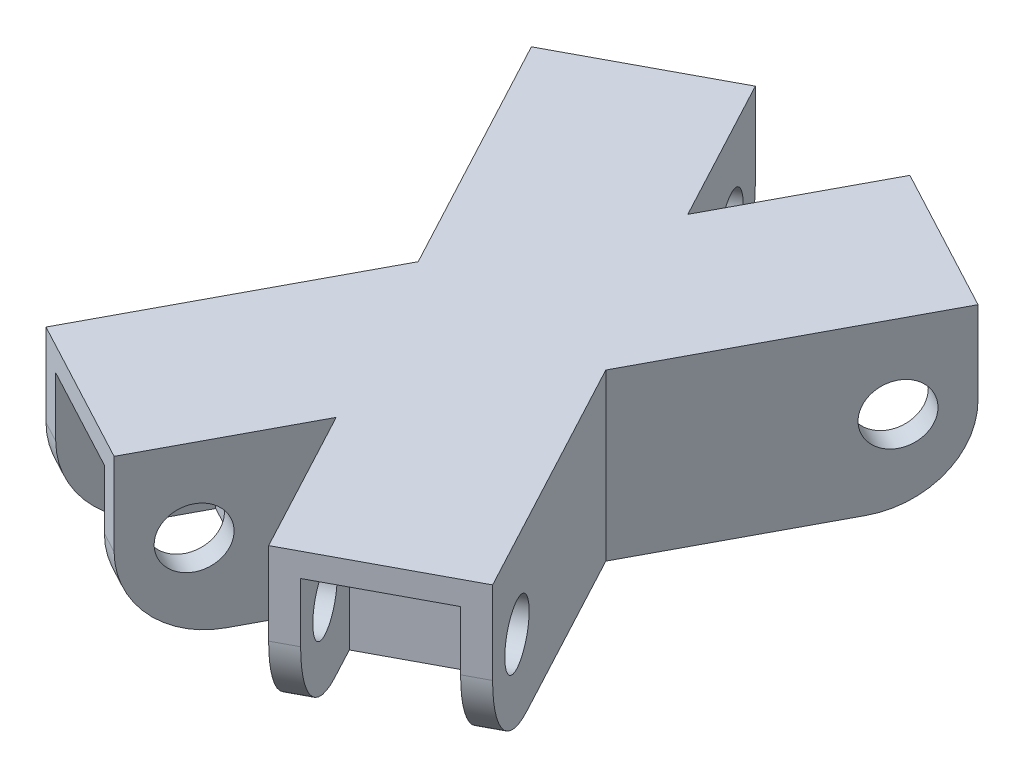
SolidWorks part; units mm, degrees
ref_plane "Front Plane" through (0, 0, 0) normal (0, 0, 1) x (1, 0, 0)
ref_plane "Top Plane" through (0, 0, 0) normal (0, 1, 0) x (1, 0, 0)
ref_plane "Right Plane" through (0, 0, 0) normal (1, 0, 0) x (0, 0, -1)
sketch "Sketch1" plane through (0, 0, 0) normal (0, 1, 0) x (1, 0, 0)
  line L0 (0, 0) -> (29.8937, 56.0234) construction
  line L1 (0, 0) -> (82.5536, 0) construction
  line L2 (0, 0) -> (-29.8937, -56.0234) construction
  line L3 (0, 0) -> (-29.8937, 56.0234) construction
  line L4 (0, 0) -> (-62.1107, 0) construction
  line L5 (0, 0) -> (29.8937, -56.0234) construction
  line L6 (-29.8937, 56.0234) -> (-18.689, 62.0021) construction
  line L7 (-29.8937, 56.0234) -> (-41.0984, 50.0446) construction
  line L8 (-41.0984, 50.0446) -> (-14.3949, 0) construction
  line L9 (-18.689, 62.0021) -> (0, 26.9773) construction
  line L10 (18.689, -62.0021) -> (41.0984, -50.0446) construction
  line L11 (29.8937, 56.0234) -> (18.689, 62.0021) construction
  line L12 (29.8937, 56.0234) -> (41.0984, 50.0446) construction
  line L13 (18.689, 62.0021) -> (0, 26.9773) construction
  line L14 (41.0984, 50.0446) -> (14.3949, 0) construction
  line L15 (-29.8937, -56.0234) -> (-18.689, -62.0021) construction
  line L16 (-29.8937, -56.0234) -> (-41.0984, -50.0446) construction
  line L17 (-14.3949, 0) -> (-41.0984, -50.0446) construction
  line L18 (14.3949, 0) -> (41.0984, -50.0446) construction
  line L19 (0, -26.9773) -> (18.689, -62.0021) construction
  line L20 (0, -26.9773) -> (-18.689, -62.0021) construction
  line L21 (47.9717, 52.135) -> (20.1528, 0)
  line L22 (20.1528, 0) -> (47.9717, -52.135)
  line L23 (16.5987, -68.8755) -> (47.9717, -52.135)
  line L24 (0, -37.7682) -> (16.5987, -68.8755)
  line L25 (0, -37.7682) -> (-16.5987, -68.8755)
  line L26 (-32.2852, -60.5052) -> (-16.5987, -68.8755)
  line L27 (-32.2852, -60.5052) -> (-47.9717, -52.135)
  line L28 (-20.1528, 0) -> (-47.9717, -52.135)
  line L29 (-47.9717, 52.135) -> (-20.1528, 0)
  line L30 (-32.2852, 60.5052) -> (-47.9717, 52.135)
  line L31 (-32.2852, 60.5052) -> (-16.5987, 68.8755)
  line L32 (-16.5987, 68.8755) -> (0, 37.7682)
  line L33 (16.5987, 68.8755) -> (0, 37.7682)
  line L34 (32.2852, 60.5052) -> (16.5987, 68.8755)
  line L35 (32.2852, 60.5052) -> (47.9717, 52.135)
  dimension "D1" = 61.916
  dimension "D2" = 63.5
  dimension "D3" = 61.916
  dimension "D4" = 63.5
  dimension "D5" = 63.5
  dimension "D6" = 63.5
  dimension "D7" = 12.7
  dimension "D8" = 12.7
  dimension "D9" = 5.08
  dimension "D10" = 12.7
  dimension "D11" = 12.7
  dimension "D12" = 90
extrude "Boss-Extrude1" add sketch "Sketch1" along normal blind 35.56
ref_plane "Plano1" through (0, 0, 0) normal (-0.8823, 0, -0.4708) x (-0.4708, 0, 0.8823)
sketch "Croquis2" plane through (0, 0, 0) normal (-0.8823, 0, -0.4708) x (-0.4708, 0, 0.8823)
  line L0 (9.4873, 0) -> (68.58, 0) construction
  line L1 (68.58, 35.56) -> (68.58, 0) construction
  line L2 (55.88, 30.48) -> (68.58, 30.48)
  line L3 (43.18, 17.78) -> (43.18, 0)
  line L4 (43.18, 0) -> (68.58, 0)
  line L5 (68.58, 0) -> (68.58, 30.48)
  arc A0 (55.88, 30.48) -> (43.18, 17.78) centre (55.88, 17.78) ccw
  dimension "D1" = 25.4
  dimension "D2" = 17.78
  dimension "D3" = 12.7
extrude "Cortar-Extruir1" cut sketch "Croquis2" against normal blind 12.7 and the other way blind 12.7
ref_plane "Plano2" through (0, 0, 0) normal (0.8823, 0, -0.4708) x (-0.4708, 0, -0.8823)
sketch "Croquis3" plane through (0, 0, 0) normal (0.8823, 0, -0.4708) x (-0.4708, 0, -0.8823)
  line L0 (-68.58, 35.56) -> (-68.58, 0) construction
  line L1 (-68.58, 0) -> (-9.4873, 0) construction
  line L2 (-55.88, 30.48) -> (-68.58, 30.48)
  line L3 (-43.18, 17.78) -> (-43.18, 0)
  line L4 (-43.18, 0) -> (-68.58, 0)
  line L5 (-68.58, 0) -> (-68.58, 30.48)
  arc A0 (-43.18, 17.78) -> (-55.88, 30.48) centre (-55.88, 17.78) ccw
  dimension "D1" = 25.4
  dimension "D2" = 12.7
  dimension "D3" = 17.78
extrude "Cortar-Extruir2" cut sketch "Croquis3" against normal blind 12.7 and the other way blind 12.7
mirror "Simetría1" about plane through (0, 0, 0) normal (0, 0, 1) of "Cortar-Extruir2", "Cortar-Extruir1"
sketch "Croquis4" plane through (-15.6865, 0, -8.3702) normal (-0.8823, 0, -0.4708) x (-0.4708, 0, 0.8823)
  line L0 (68.58, 35.56) -> (68.58, 0) construction
  line L1 (9.4873, 0) -> (68.58, 0) construction
  circle A0 centre (55.88, 17.78) radius 6.35
  dimension "D1" = 12.7
  dimension "D2" = 12.7
  dimension "D3" = 17.78
extrude "Cortar-Extruir3" cut sketch "Croquis4" against normal blind 35.56
mirror "Simetría2" about plane through (0, 0, 0) normal (1, 0, 0) of "Cortar-Extruir3"
mirror "Simetría7" about plane through (0, 0, 0) normal (0, 0, 1) of "Simetría2", "Cortar-Extruir3"
fillet "Redondeo1" radius 17.78 8 edges at (45.7308, 0, 53.3307) (18.8396, 0, 67.6797) (-18.8396, 0, 67.6797) (-45.7308, 0, 53.3307) (-45.7308, 0, -53.3307) (-18.8396, 0, -67.6797) (18.8396, 0, -67.6797) (45.7308, 0, -53.3307)
